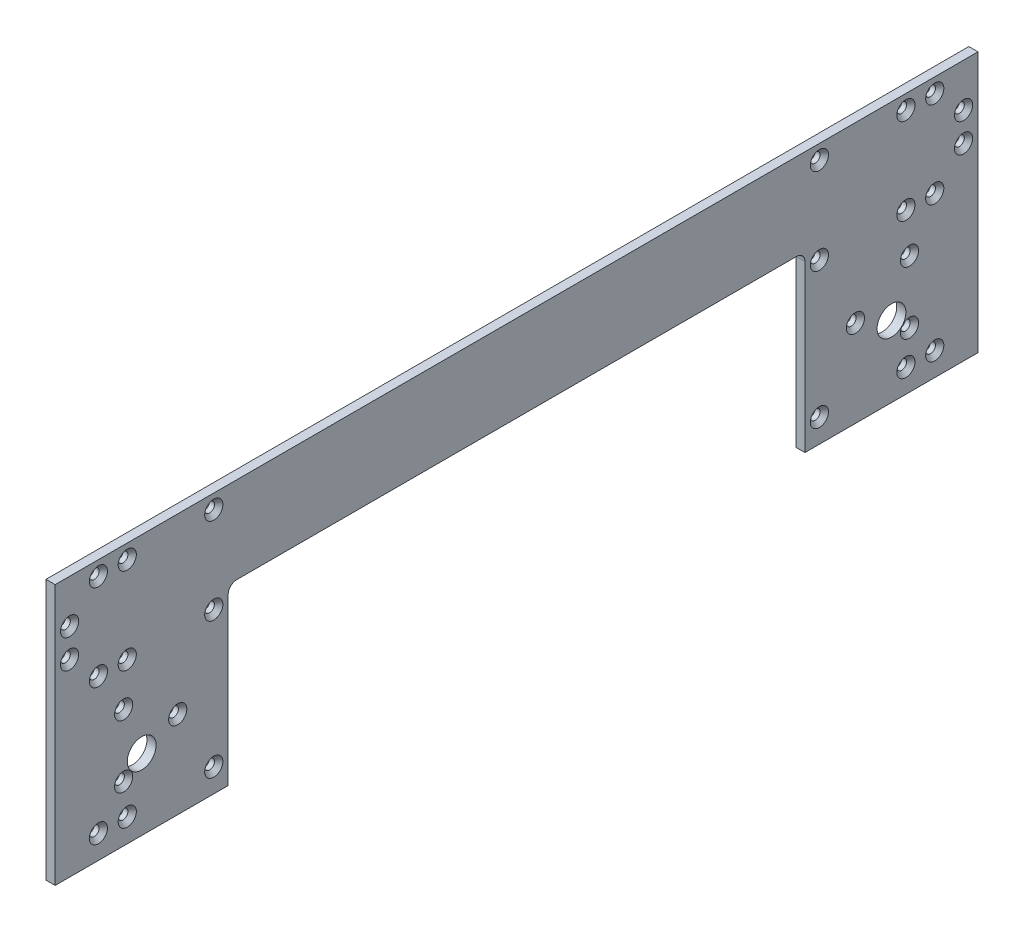
SolidWorks part; units mm, degrees
material "Garolite (G-10/FR4)"
ref_plane "Front Plane" through (0, 0, 0) normal (0, 0, 1) x (1, 0, 0)
ref_plane "Top Plane" through (0, 0, 0) normal (0, 1, 0) x (1, 0, 0)
ref_plane "Right Plane" through (0, 0, 0) normal (1, 0, 0) x (0, 0, -1)
sketch "Sketch1" plane through (0, 0, 0) normal (1, 0, 0) x (0, 0, -1)
  line L0 (160, 0) -> (160, 3.175)
  line L1 (-160, 0) -> (160, 0)
  line L2 (160, 3.175) -> (160, 47.175)
  line L3 (-160, 90.35) -> (160, 90.35)
  line L4 (-160, 3.175) -> (-160, 47.175)
  line L5 (-160, 3.175) -> (-160, 0)
  line L6 (160, 47.175) -> (160, 50.35)
  line L7 (160, 50.35) -> (160, 60.35)
  line L8 (160, 60.35) -> (160, 90.35)
  line L9 (-160, 47.175) -> (-160, 50.35)
  line L10 (-160, 50.35) -> (-160, 60.35)
  line L11 (-160, 60.35) -> (-160, 90.35)
  dimension "D1" = 320
  dimension "D2" = 30
  dimension "D3" = 3.175
  dimension "D4" = 44
  dimension "D5" = 3.175
  dimension "D6" = 10
extrude "Boss-Extrude1" add sketch "Sketch1" along normal blind 3.175
hole_wizard "CSK for M3 Flat Head Machine Screw1" positions "Sketch3" profile "Sketch2" countersink size "M3" standard "Ansi Metric" end condition through all
sketch "Sketch3" plane through (3.175, 0, 0) normal (1, 0, 0) x (0, 0, -1)
  line L0 (-105, 8.175) -> (-160, 8.175) construction
  line L1 (-160, 90.35) -> (-160, 0) construction
  line L3 (-160, 0) -> (160, 0) construction
  line L4 (-105, 55.35) -> (-160, 55.35) construction
  line L5 (-130, 30.175) -> (-117.5, 30.175) construction
  line L7 (-136.25, 19.3497) -> (-130, 30.175) construction
  line L8 (-130, 30.175) -> (-136.25, 41.0003) construction
  line L10 (-145, 8.175) -> (-145, 85.35) construction
  line L12 (-135, 8.175) -> (-135, 85.35) construction
  line L14 (-105, 8.175) -> (-105, 85.35) construction
  line L16 (-105, 85.35) -> (-160, 85.35) construction
  line L18 (-155, 65.35) -> (-155, 75.35)
  circle A0 centre (-130, 30.175) radius 12.5 construction
  point P0 (-145, 8.175)
  point P1 (-135, 8.175)
  point P3 (-105, 8.175)
  point P15 (-145, 55.35)
  point P17 (-135, 55.35)
  point P19 (-105, 55.35)
  point P38 (-117.5, 30.175)
  point P40 (-136.25, 19.3497)
  point P42 (-136.25, 41.0003)
  point P55 (-145, 85.35)
  point P57 (-135, 85.35)
  point P59 (-105, 85.35)
  point P86 (-155, 65.35)
  point P88 (-155, 75.35)
  dimension "D11" = 25
  dimension "D1" = 8.175
  dimension "D2" = 15
  dimension "D3" = 10
  dimension "D4" = 30
  dimension "D5" = 30
  dimension "D6" = 10
  dimension "D7" = 10
  dimension "D8" = 55.35
  dimension "D9" = 30.175
  dimension "D10" = 30
  dimension "D12" = 120
  dimension "D13" = 120
  dimension "D14" = 10
sketch "Sketch2" plane through (3.175, 8.175, 145) normal (0, 1, 0) x (0, 0, -1)
  line L0 (0, 0) -> (0, 3.175)
  line L1 (0, 3.175) -> (1.7, 3.175)
  line L2 (1.7, 3.175) -> (1.7, 1.45)
  line L3 (1.7, 1.45) -> (3.15, 0)
  line L5 (3.15, 0) -> (0, 0)
  line L6 (-1.7, 1.45) -> (-3.15, 0) construction
  line L11 (0, -6.35) -> (0, 107.95) construction
  dimension "Thru Hole Dia." = 3.4
  dimension "Thru Hole Depth" = 3.175
  dimension "Near C'Sink Dia." = 6.3
  dimension "Near C'Sink Angle" = 90
mirror "Mirror1" about plane through (0, 0, 0) normal (0, 0, 1) of "CSK for M3 Flat Head Machine Screw1"
sketch "Sketch4" plane through (3.175, 0, 0) normal (1, 0, 0) x (0, 0, -1)
  line L0 (-100, 57.35) -> (-100, 0)
  line L1 (-160, 0) -> (160, 0) construction
  line L2 (-160, 90.35) -> (-160, 0) construction
  line L3 (-97, 60.35) -> (97, 60.35)
  line L4 (0, 60.35) -> (0, 0) construction
  line L5 (100, 0) -> (-100, 0)
  line L6 (100, 57.35) -> (100, 0)
  line L7 (-130, 24.675) -> (130, 24.675) construction
  line L8 (160, 0) -> (160, 90.35) construction
  arc A0 (-100, 57.35) -> (-97, 60.35) centre (-97, 57.35) cw
  arc A1 (100, 57.35) -> (97, 60.35) centre (97, 57.35) ccw
  circle A2 centre (-130, 24.675) radius 5
  circle A3 centre (130, 24.675) radius 5
  dimension "D3" = 3
  dimension "D4" = 10
  dimension "D1" = 60
  dimension "D2" = 60.35
  dimension "D5" = 30
  dimension "D6" = 24.675
  dimension "D7" = 30
extrude "Cut-Extrude1" cut sketch "Sketch4" against normal through all
